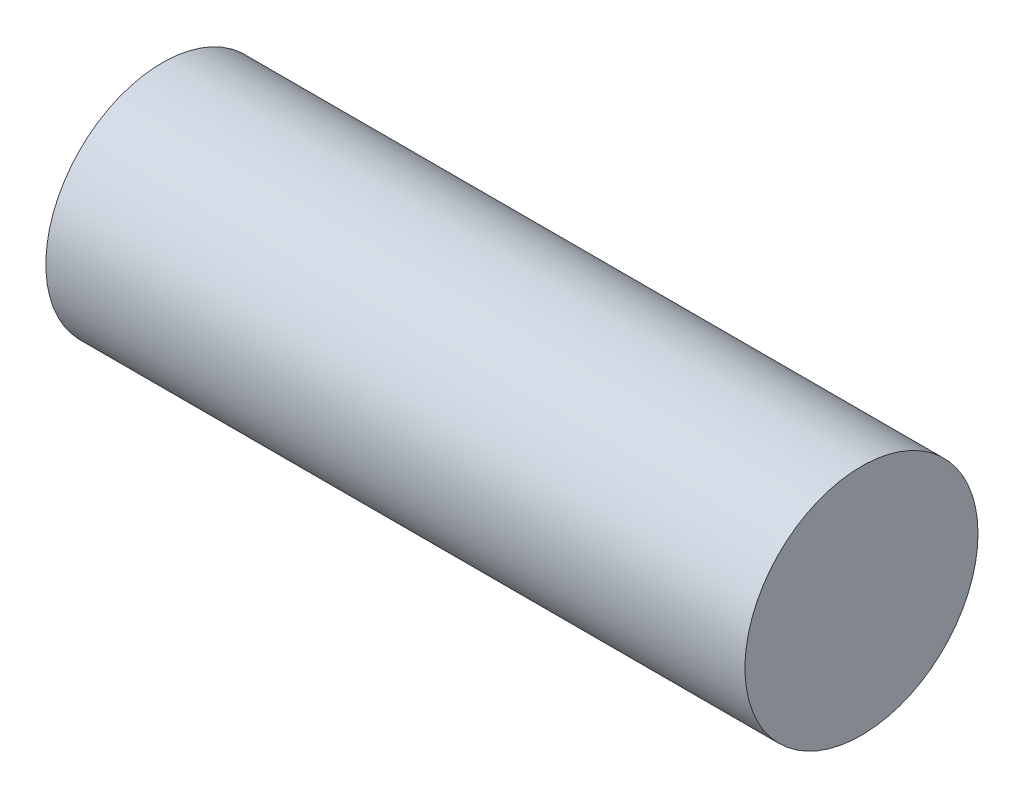
SolidWorks part; units mm, degrees
ref_plane "Front Plane" through (0, 0, 0) normal (0, 0, 1) x (1, 0, 0)
ref_plane "Top Plane" through (0, 0, 0) normal (0, 1, 0) x (1, 0, 0)
ref_plane "Right Plane" through (0, 0, 0) normal (1, 0, 0) x (0, 0, -1)
sketch "Sketch1" plane through (0, 0, 0) normal (1, 0, 0) x (0, 0, -1)
  circle A0 centre (0, 0) radius 5
  dimension "D1" = 10
extrude "Boss-Extrude1" add sketch "Sketch1" along normal blind 30
